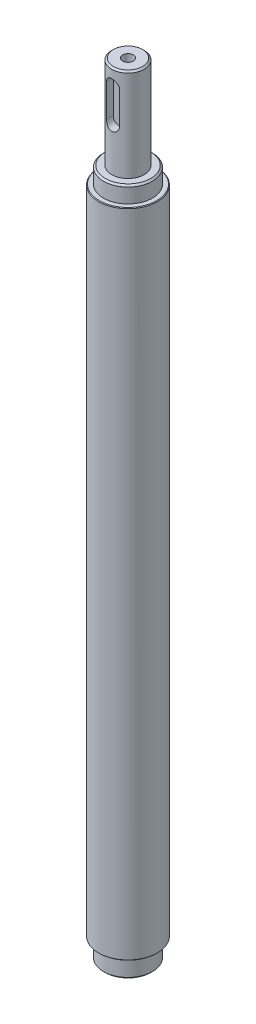
SolidWorks part; units mm, degrees
material "Q235-A"
ref_plane "前视基准面" through (0, 0, 0) normal (0, 0, 1) x (1, 0, 0)
ref_plane "上视基准面" through (0, 0, 0) normal (0, 1, 0) x (1, 0, 0)
ref_plane "右视基准面" through (0, 0, 0) normal (1, 0, 0) x (0, 0, -1)
sketch "草图1" plane through (0, 0, 0) normal (0, 0, 1) x (1, 0, 0)
  line L0 (0, 0) -> (0, -254.9533) construction
  line L2 (0, 0) -> (0, -239.5)
  line L3 (0, -239.5) -> (-7.5, -239.5)
  line L4 (-7.5, -239.5) -> (-7.5, -233.5)
  line L5 (-7.5, -233.5) -> (-9, -233.5)
  line L7 (-9, -33.5) -> (-7.5, -33.5)
  line L8 (-7.5, -33.5) -> (-7.5, -28.5)
  line L12 (-9, -233.5) -> (-9, -33.5)
  line L16 (-7.5, -28.5) -> (-5, -28.5)
  line L19 (-5, -28.5) -> (-5, 0)
  line L20 (-5, 0) -> (0, 0)
  dimension "D16" = 28.5
  dimension "D2" = 200
  dimension "D3" = 15
  dimension "D4" = 10
  dimension "D5" = 18
  dimension "D7" = 6
  dimension "D8" = 5
revolve "旋转1" add sketch "草图1" angle 360 about L2
chamfer "倒角1" distance 0.5 angle 45 3 edges at (-7.5, -239.5, 0) (-7.5, -28.5, 0) (-5, 0, 0)
chamfer "倒角2" distance 0.2 angle 45 2 edges at (-9, -233.5, 0) (-9, -33.5, 0)
ref_plane "基准面1" through (0, 0, -9) normal (0, 0, 1) x (1, 0, 0)
sketch "草图4" plane through (0, 0, -9) normal (0, 0, 1) x (1, 0, 0)
  line L0 (0, 80.5) -> (0, -80.5)
  point P3 (0, 32.5)
  point P4 (0, -32.5)
  dimension "D1" = 48
  dimension "D2" = 48
  dimension "D3" = 32.5
hole_wizard "Ø6.0 (6) 直径孔1" positions "草图6" profile "草图5" hole size "Ø6.0" standard "GB"
sketch "草图6" plane through (0, 0, -9) normal (0, 0, 1) x (1, 0, 0)
  line L1 (0, 0) -> (0, -269.1262) construction
  line L3 (9, -133.5) -> (-66.6543, -133.5) construction
  line L4 (9, -233.3) -> (9, -33.7) construction
  point P0 (0, -214)
  point P3 (0, -166)
  point P6 (0, -101)
  point P9 (0, -53)
  dimension "D1" = 32.5
  dimension "D2" = 48
  dimension "D3" = 32.5
  dimension "D4" = 48
sketch "草图5" plane through (0, -214, -9) normal (1, 0, 0) x (0, 1, 0)
  line L0 (0, 0) -> (0, 3.8026)
  line L1 (0, 3.8026) -> (3, 2)
  line L2 (3, 2) -> (3, 0)
  line L5 (3, 0) -> (0, 0)
  line L10 (0, 3.8026) -> (-3, 2) construction
  line L11 (0, -6.35) -> (0, 107.95) construction
  dimension "孔直径" = 6
  dimension "孔深度" = 2
  dimension "导头角度" = 118
pattern_circular "阵列(圆周)1" count 2 over 90 about axis through (0, 0, 0) along (0, 1, 0) of "Ø6.0 (6) 直径孔1"
sketch "草图3" plane through (0, 0, 0) normal (0, 1, 0) x (1, 0, 0)
  line L1 (-6.6073, 9.3914) -> (9.8332, 9.3914)
  line L2 (-6.6073, 9.3914) -> (-6.6073, 4)
  line L3 (-6.6073, 4) -> (9.8332, 4)
  line L4 (9.8332, 9.3914) -> (9.8332, 4)
  dimension "D1" = 4
extrude "切除-拉伸2" [suppressed] cut sketch "草图3" against normal blind 15
ref_plane "基准面2" through (0, 0, 2.5) normal (0, 0, 1) x (1, 0, 0)
sketch "草图7" plane through (0, 0, 2.5) normal (0, 0, 1) x (1, 0, 0)
  line L0 (0, -5) -> (0, -15) construction
  line L1 (2, -5) -> (2, -15)
  line L2 (-2, -5) -> (-2, -15)
  line L3 (4.5, 0) -> (-4.5, 0) construction
  arc A0 (2, -5) -> (-2, -5) centre (0, -5) ccw
  arc A1 (-2, -15) -> (2, -15) centre (0, -15) ccw
  point P3 (0, -10)
  dimension "D1" = 4
  dimension "D2" = 10
  dimension "D3" = 5
extrude "切除-拉伸3" cut sketch "草图7" along normal blind 10
hole_wizard "M4 螺纹孔1" positions "草图9" profile "草图8" tap size "M4" standard "GB"
sketch "草图9" plane through (0, 0, 0) normal (0, 1, 0) x (1, 0, 0)
  point P0 (0, 0)
sketch "草图8" plane through (0, 0, 0) normal (1, 0, 0) x (0, 0, 1)
  line L0 (0, 0) -> (0, 12.4914)
  line L1 (0, 12.4914) -> (1.65, 11.5)
  line L2 (1.65, 11.5) -> (1.65, 0)
  line L5 (1.65, 0) -> (0, 0)
  line L10 (0, 12.4914) -> (-1.65, 11.5) construction
  line L11 (0, -6.35) -> (0, 107.95) construction
  dimension "螺纹孔钻头直径" = 3.3
  dimension "螺纹孔钻头深度" = 11.5
  dimension "导头角度" = 118
cosmetic thread "孔螺蚊线1" parameters "D1"=8, "D2"=4
